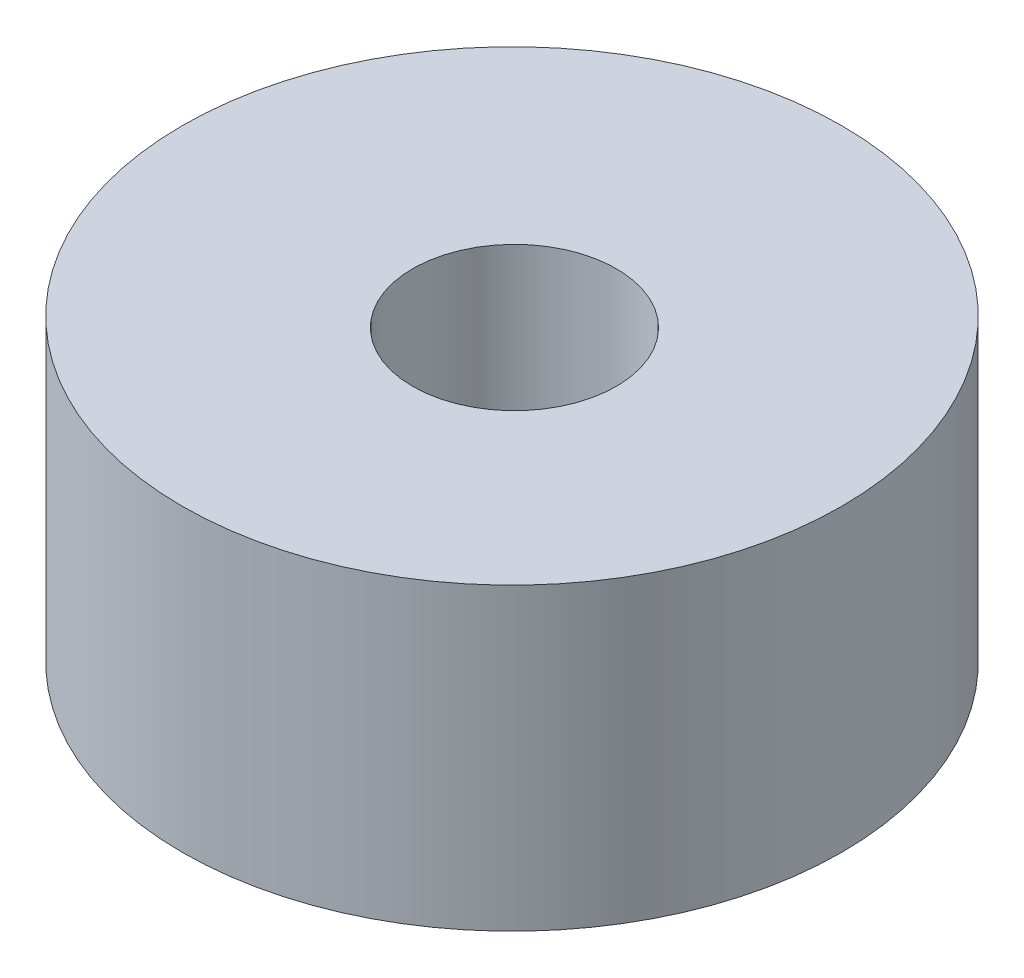
SolidWorks part; units mm, degrees
ref_plane "Front Plane" through (0, 0, 0) normal (0, 0, 1) x (1, 0, 0)
ref_plane "Top Plane" through (0, 0, 0) normal (0, 1, 0) x (1, 0, 0)
ref_plane "Right Plane" through (0, 0, 0) normal (1, 0, 0) x (0, 0, -1)
sketch "Sketch1" plane through (0, 0, 0) normal (0, 1, 0) x (1, 0, 0)
  circle A0 centre (0, 0) radius 11
extrude "Boss-Extrude1" add sketch "Sketch1" along normal blind 10
hole_wizard "M8 Tapped Hole1" positions "3DSketch1" profile "Sketch2" tap size "M8" standard "DIN"
sketch3d "3DSketch1"
  point P0 (0, 0, 0)
  point P3 (0, 0, 0)
  point P6 (1.3393, 47.7984, 0)
  point P8 (0.3757, 10, 0.2932)
  point P10 (0.3757, 10, 0.2932)
  point P12 (0.3757, 10, 0.2932)
sketch "Sketch2" plane through (0.3757, 10, 0.2932) normal (1, 0, 0) x (0, 0, 1)
  line L0 (0, 0) -> (0, 10)
  line L1 (0, 10) -> (3.4, 10)
  line L2 (3.4, 10) -> (3.4, 0)
  line L5 (3.4, 0) -> (0, 0)
  line L11 (0, -6.35) -> (0, 107.95) construction
  dimension "Thru Tap Drill Dia." = 6.8
  dimension "Thru Tap Drill Depth" = 10
cosmetic thread "Hole Thread1" parameters "D2"=8
cosmetic thread "Hole Thread2" parameters "D2"=8
cosmetic thread "Hole Thread3" parameters "D2"=8
cosmetic thread "Hole Thread4" parameters "D2"=8
cosmetic thread "Hole Thread5" parameters "D2"=8
cosmetic thread "Hole Thread6" parameters "D2"=8
